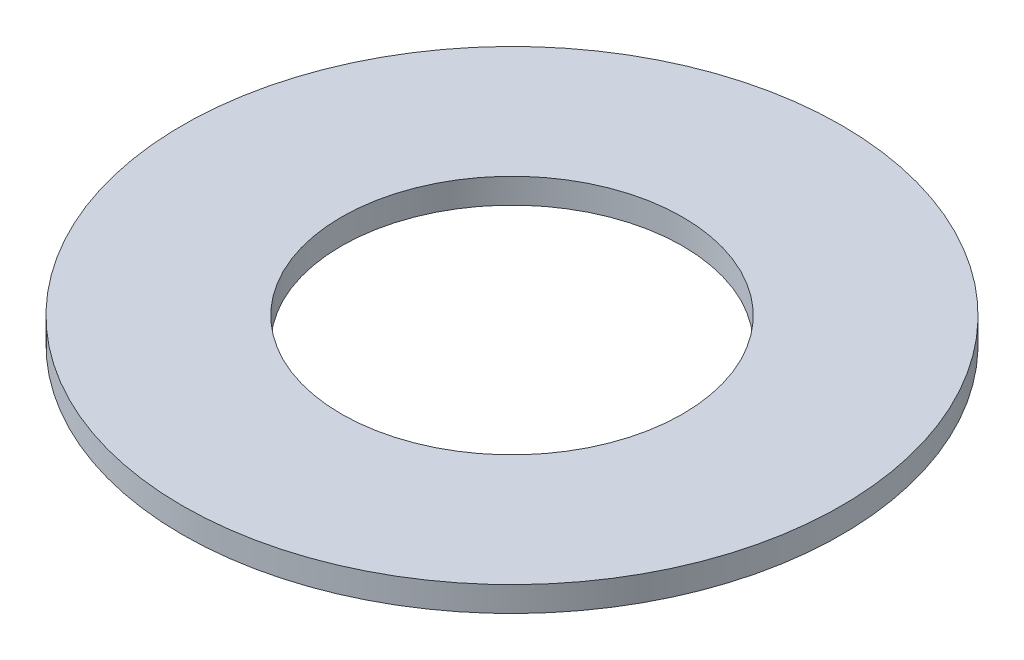
SolidWorks part; units mm, degrees
ref_plane "Front Plane" through (0, 0, 0) normal (0, 0, 1) x (1, 0, 0)
ref_plane "Top Plane" through (0, 0, 0) normal (0, 1, 0) x (1, 0, 0)
ref_plane "Right Plane" through (0, 0, 0) normal (1, 0, 0) x (0, 0, -1)
sketch "Sketch1" plane through (0, 0, 0) normal (0, 1, 0) x (1, 0, 0)
  circle A0 centre (0, 0) radius 44.45
  dimension "OD" = 88.9
extrude "Boss-Extrude1" add sketch "Sketch1" along normal blind 3.3782
sketch "Sketch5" plane through (0, 3.3782, 0) normal (0, 1, 0) x (-1, 0, 0)
  circle A0 centre (0, 0) radius 23.0124
  dimension "ID" = 46.0248
extrude "Cut-Extrude1" cut sketch "Sketch5" against normal through all
